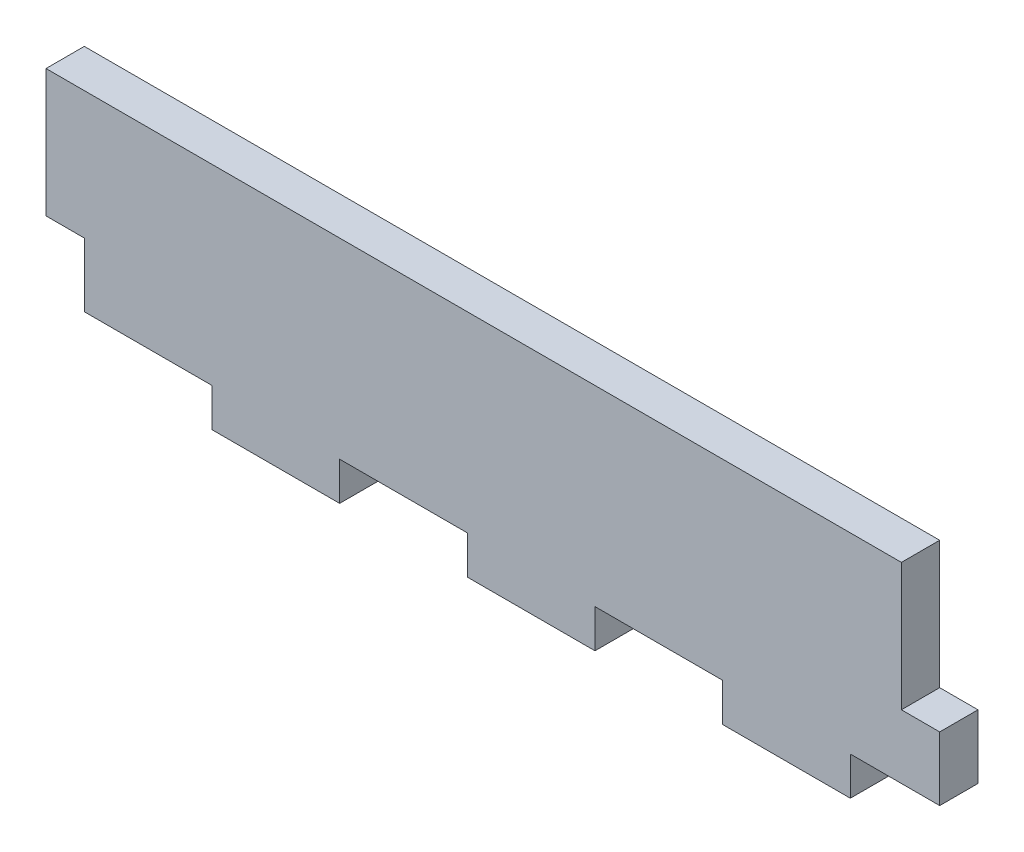
SolidWorks part; units mm, degrees
ref_plane "Plan de face" through (0, 0, 0) normal (0, 0, 1) x (1, 0, 0)
ref_plane "Plan de dessus" through (0, 0, 0) normal (0, 1, 0) x (1, 0, 0)
ref_plane "Plan de droite" through (0, 0, 0) normal (1, 0, 0) x (0, 0, -1)
sketch "Esquisse1" plane through (0, 0, 0) normal (0, 0, 1) x (1, 0, 0)
  line L1 (0, 0) -> (67, 0)
  line L2 (0, 0) -> (0, -18)
  line L3 (0, -18) -> (67, -18)
  line L4 (67, 0) -> (67, -18)
  dimension "D1" = 18
  dimension "D2" = 67
extrude "Boss.-Extru.1" add sketch "Esquisse1" along normal blind 3
sketch "Esquisse2" plane through (0, 0, 3) normal (0, 0, 1) x (1, 0, 0)
  line L1 (0, -18) -> (10, -18)
  line L2 (0, -18) -> (0, -15)
  line L3 (0, -15) -> (10, -15)
  line L4 (10, -18) -> (10, -15)
  dimension "D1" = 3
  dimension "D2" = 10
extrude "Enlèv. mat.-Extru.1" cut sketch "Esquisse2" against normal blind 10
pattern_linear "Répétition linéaire1" count 4 spacing 20 along (1, 0, 0) of "Enlèv. mat.-Extru.1"
sketch "Esquisse3" plane through (0, 0, 3) normal (0, 0, 1) x (1, 0, 0)
  line L1 (67, 0) -> (64, 0)
  line L2 (67, 0) -> (67, -10)
  line L3 (67, -10) -> (64, -10)
  line L4 (64, 0) -> (64, -10)
  dimension "D1" = 3
  dimension "D2" = 10
extrude "Enlèv. mat.-Extru.2" cut sketch "Esquisse3" against normal blind 10
sketch "Esquisse4" plane through (0, 0, 0) normal (-1, 0, 0) x (0, 0, 1)
  line L0 (3, 0) -> (3, -15) construction
  line L1 (0, 0) -> (3, 0)
  line L2 (0, 0) -> (0, -10)
  line L3 (0, -10) -> (3, -10)
  line L4 (3, 0) -> (3, -10)
  dimension "D1" = 10
extrude "Boss.-Extru.2" add sketch "Esquisse4" along normal blind 3
